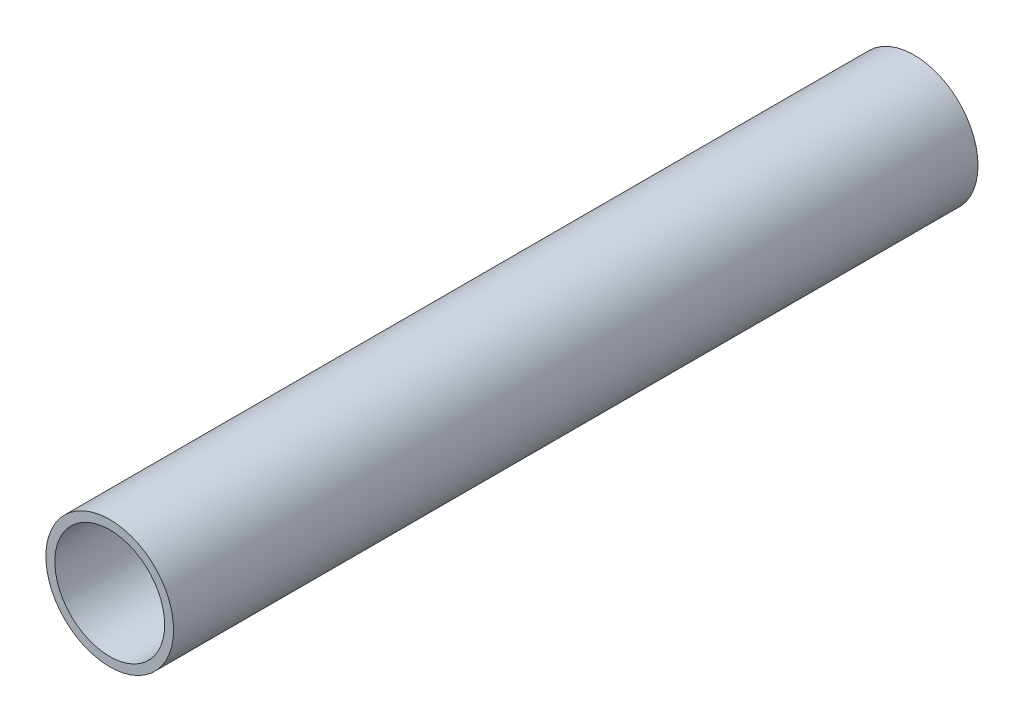
SolidWorks part; units mm, degrees
material "6063-T6, Rod (SS)"
ref_plane "Front Plane" through (0, 0, 0) normal (0, 0, 1) x (1, 0, 0)
ref_plane "Top Plane" through (0, 0, 0) normal (0, 1, 0) x (1, 0, 0)
ref_plane "Right Plane" through (0, 0, 0) normal (1, 0, 0) x (0, 0, -1)
sketch "Sketch1" plane through (0, 0, 0) normal (0, 0, 1) x (1, 0, 0)
  circle A0 centre (0, 0) radius 6.35
  circle A1 centre (0, 0) radius 5.461
  dimension "D1" = 12.7
  dimension "D2" = 10.922
extrude "Boss-Extrude1" add sketch "Sketch1" along normal blind 80
